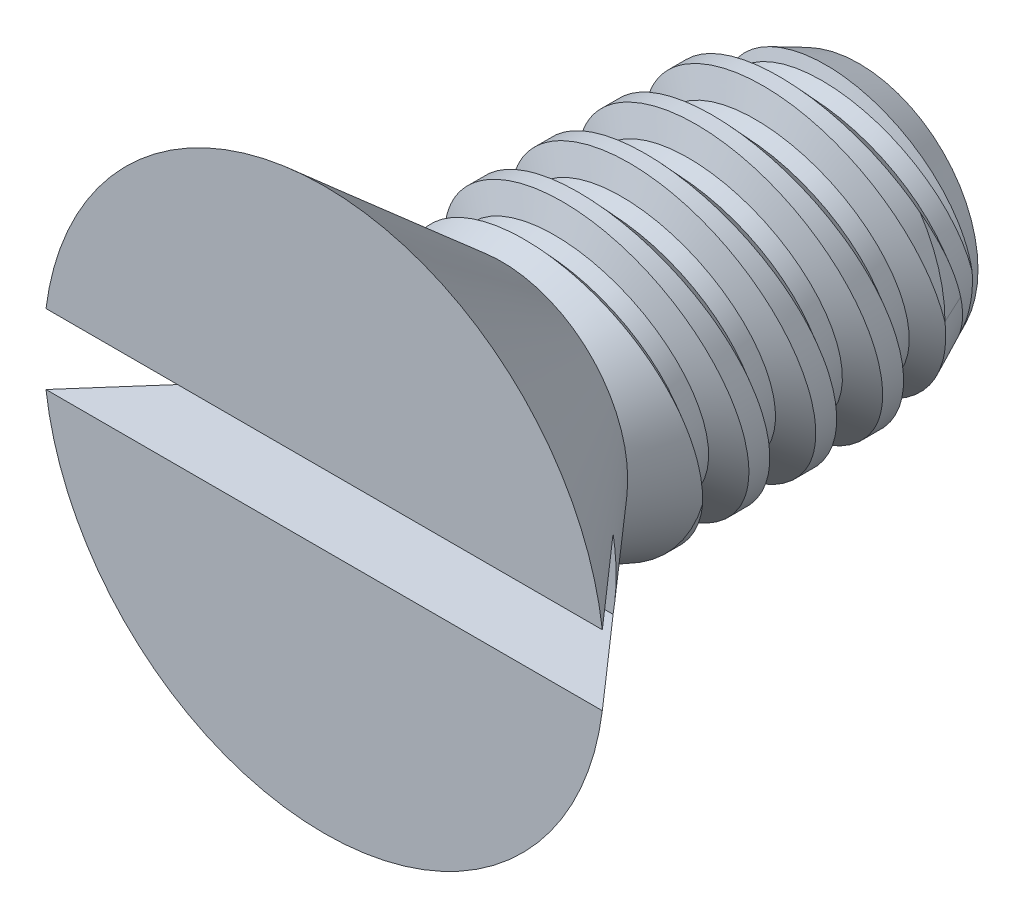
SolidWorks part; units mm, degrees
ref_plane "Front" through (0, 0, 0) normal (0, 0, 1) x (1, 0, 0)
ref_plane "Top" through (0, 0, 0) normal (0, 1, 0) x (1, 0, 0)
ref_plane "Right" through (0, 0, 0) normal (1, 0, 0) x (0, 0, -1)
sketch "Sketch1" plane through (0, 0, 0) normal (0, 0, 1) x (1, 0, 0)
  circle A0 centre (0, 0) radius 3.3274
  dimension "Head Dia" = 6.6548
extrude "Extrude3" add sketch "Sketch1" along normal blind 2.1082
sketch "Sketch11" plane through (0, 0, 0) normal (1, 0, 0) x (0, 0, -1)
  line L0 (0.4414, 0) -> (-2.8754, 0) construction
  line L2 (0, 1.4948) -> (-2.1082, 3.3274)
  line L3 (0, -3.3274) -> (0, 3.3274) construction
  line L5 (-2.1082, 3.3274) -> (0, 3.3274)
  line L7 (0, 3.3274) -> (0, 1.4948)
  line L8 (0, 3.3274) -> (-2.1082, 3.3274) construction
  line L10 (-2.1082, 3.3274) -> (-2.1082, -3.3274) construction
  line L11 (0, -1.4948) -> (-2.1082, -3.3274) construction
  dimension "D1" = 82
revolve "Cut-Revolve3" cut sketch "Sketch11" angle 360 about L0
sketch "Sketch4" plane through (0, 0, 0) normal (1, 0, 0) x (0, 0, -1)
  line L0 (0, 0) -> (4.2418, 0)
  line L2 (4.2418, -1.7526) -> (0, -1.7526) construction
  line L3 (4.2418, 0) -> (4.2418, 1.7526)
  line L4 (4.2418, 1.7526) -> (0, 1.7526)
  line L5 (-2.1082, 3.3274) -> (-2.1082, -3.3274) construction
  line L6 (0, 1.7526) -> (0, 0)
  line L7 (4.2418, 0) -> (6.7818, 0) construction
  dimension "D1" = 2.54
  dimension "Screw Dia" = 3.5052
  dimension "Screw Length" = 6.35
  dimension "Body Length" = 4.2418
revolve "Revolve1" add sketch "Sketch4" angle 360 about L7
sketch "Sketch5" plane through (0, 0, 0) normal (1, 0, 0) x (0, 0, -1)
  line L0 (0, 1.7526) -> (0.0968, 1.7745) construction
  line L1 (0, 1.7526) -> (0, -1.7526) construction
  line L2 (0.0968, 1.7745) -> (0.4336, 1.4103)
  line L3 (0.4336, 1.4103) -> (0.6271, 1.4541)
  line L4 (0.6271, 1.4541) -> (0.7741, 1.9279)
  line L5 (0.7741, 1.9279) -> (0.0968, 1.7745)
  line L6 (0.5303, 1.4322) -> (0.4355, 1.8512) construction
  line L7 (0, 1.7526) -> (0, 0) construction
  line L8 (0, -1.7526) -> (0.7938, -1.7526) construction
  line L11 (0.7938, -1.7526) -> (0, 1.7526) construction
  line L12 (4.2418, 1.7526) -> (0, 1.7526) construction
  line L13 (4.2418, -1.7526) -> (0, -1.7526) construction
  line L14 (0.4578, 1.7526) -> (1.2515, -1.7526) construction
  line L15 (0, -0.1935) -> (1.7093, 0.1935) construction
  point P22 (0.8547, 0)
  dimension "D1" = 0.7937
  dimension "Pitch" = 0.7937
  dimension "D2" = 0.0992
  dimension "D3" = 0.1984
  dimension "D4" = 60
revolve "Cut-Revolve1" cut sketch "Sketch5" angle 360 about L15
sketch "Sketch13" plane through (0, 0, 0) normal (1, 0, 0) x (0, 0, -1)
  line L0 (4.2418, 1.4103) -> (3.5077, 1.7526)
  line L1 (4.2418, 0) -> (4.2418, 1.7526) construction
  line L2 (3.5077, 1.7526) -> (4.2418, 1.7526)
  line L3 (4.2418, 1.7526) -> (4.2418, 1.4103)
  line L4 (4.2418, 1.7526) -> (0, 1.7526) construction
  line L5 (0, 0) -> (3.5077, 0) construction
  line L6 (0, 0) -> (4.2418, 0) construction
  line L7 (3.5077, 1.7526) -> (3.5077, -1.7526) construction
  dimension "D1" = 25
  dimension "D2" = 3.5052
revolve "Cut-Revolve4" cut sketch "Sketch13" angle 360 about L5
sketch "Sketch16" plane through (0, 0, 0) normal (1, 0, 0) x (0, 0, -1)
  line L0 (0, 1.4948) -> (0.7084, 1.7526)
  line L1 (0.7084, 1.7526) -> (0, 1.7526)
  line L2 (0, 1.7526) -> (0, 1.4948)
  line L3 (0, 1.7526) -> (0, 0) construction
  line L4 (4.2418, 1.7526) -> (0, 1.7526) construction
  line L5 (0, 1.4948) -> (-2.1082, 3.3274) construction
  line L6 (0, 1.4948) -> (-2.1082, 3.3274) construction
  line L7 (0, 0) -> (4.2418, 0) construction
  line L8 (0, 0) -> (4.2418, 0) construction
  dimension "D1" = 20
revolve "Cut-Revolve5" cut sketch "Sketch16" angle 360 about L8
pattern_linear "LPattern2" count 5 spacing 0.7937 along (0, 0, -1)
sketch "Sketch15" plane through (0, 0, 2.1082) normal (0, 0, 1) x (1, 0, 0)
  line L0 (-3.3274, 0.4159) -> (3.3274, -0.4159) construction
  line L1 (-3.3274, 0.4159) -> (3.3274, 0.4159)
  line L2 (-3.3274, 0.4159) -> (-3.3274, -0.4159)
  line L3 (-3.3274, -0.4159) -> (3.3274, -0.4159)
  line L4 (3.3274, 0.4159) -> (3.3274, -0.4159)
  circle A0 centre (0, 0) radius 3.3274 construction
  dimension "Slot Width" = 0.8318
extrude "Cut-Extrude5" cut sketch "Sketch15" against normal blind 1.0541
equation "\"D2@Sketch5\"=\"Pitch@Sketch5\"/8"
equation "\"D3@Sketch5\"=\"Pitch@Sketch5\"/4"
equation "\"D3@LPattern2\"=\"Pitch@Sketch5\""
equation "\"D1@LPattern2\"=\"Body Length@Sketch4\"/\"Pitch@Sketch5\""
equation "\"D1@Sketch5\"=\"Pitch@Sketch5\""
equation "\"Slot Width@Sketch15\"=\"Head Dia@Sketch1\"/8"
equation "\"Slot Depth@Cut-Extrude5\"=\"Head Ht@Extrude3\"/ 2"
